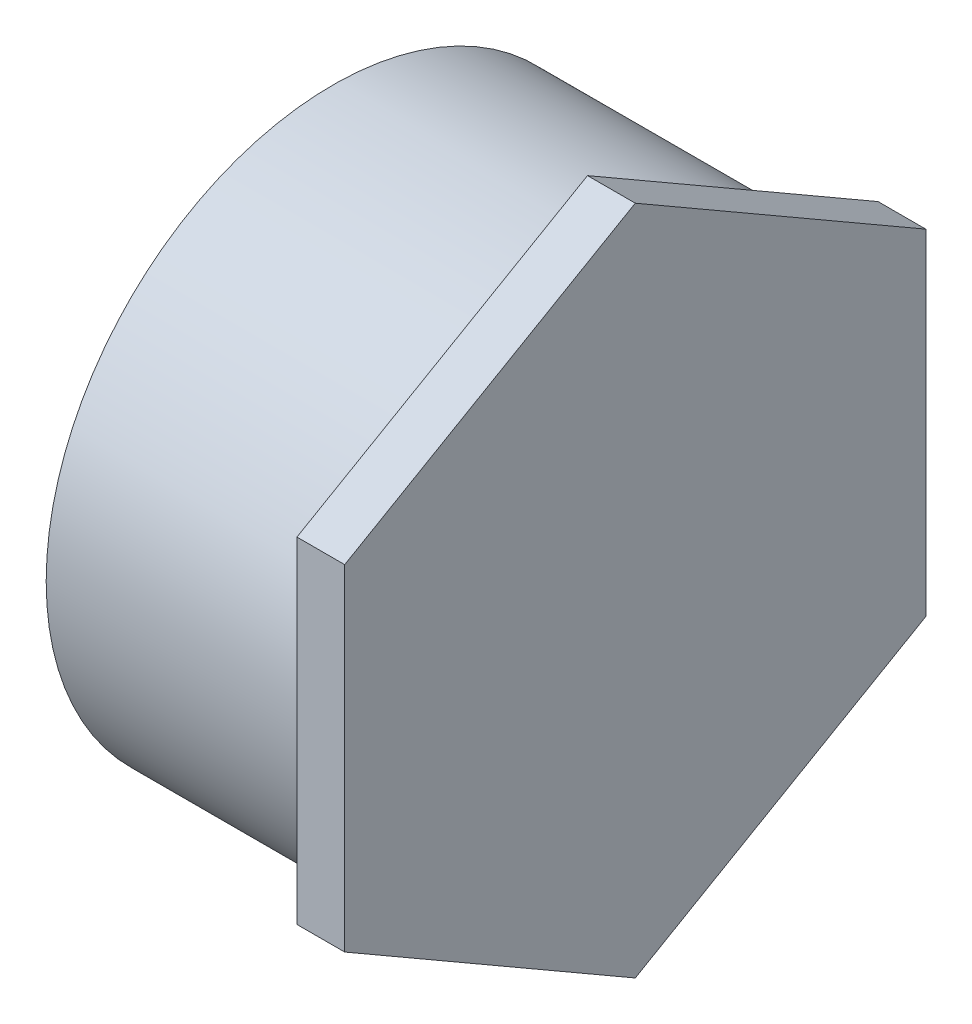
SolidWorks part; units mm, degrees
material "PVC Rigid"
ref_plane "Front Plane" through (0, 0, 0) normal (0, 0, 1) x (1, 0, 0)
ref_plane "Top Plane" through (0, 0, 0) normal (0, 1, 0) x (1, 0, 0)
ref_plane "Right Plane" through (0, 0, 0) normal (1, 0, 0) x (0, 0, -1)
sketch "Sketch0" plane through (0, 0, 0) normal (0, 0, 1) x (1, 0, 0)
  line L2 (-30.1625, 57.15) -> (-30.1625, -57.15) construction
  line L3 (-30.1625, 0) -> (30.1625, 0) construction
  line L14 (20.6375, 51.1302) -> (20.6375, -51.1302) construction
  point P5 (20.6375, 0)
  dimension "ID" = 102.2604
  dimension "L" = 60.325
  dimension "C" = 50.8
  dimension "Pipe OD" = 114.3
  dimension "R" = 9.525
  dimension "Wall Thickness" = 6.0198
sketch "Sketch1" plane through (0, 0, 0) normal (0, 0, 1) x (1, 0, 0)
  line L0 (-30.1625, -57.15) -> (30.1625, -57.15)
  line L1 (-30.1625, 0) -> (30.1625, 0) construction
  line L3 (30.1625, 0) -> (20.6375, 0)
  line L4 (20.6375, -51.1302) -> (-30.1625, -51.1302)
  line L5 (-30.1625, -51.1302) -> (-30.1625, -57.15)
  line L6 (-30.1625, 57.15) -> (-30.1625, -57.15) construction
  line L7 (30.1625, 0) -> (30.1625, -57.15)
  line L10 (20.6375, 0) -> (20.6375, -51.1302)
revolve "Revolve1" add sketch "Sketch1" angle 360 about L1
sketch "Sketch2" plane through (30.1625, 0, 0) normal (1, 0, 0) x (0, 0, -1)
  line L0 (0, 66.9077) -> (0, 0) construction
  line L1 (0, 66.9077) -> (-57.9437, 33.4538)
  line L2 (-57.9437, 33.4538) -> (-57.9437, -33.4538)
  line L3 (-57.9437, -33.4538) -> (0, -66.9077)
  line L4 (0, -66.9077) -> (57.9437, -33.4538)
  line L5 (57.9437, -33.4538) -> (57.9437, 33.4538)
  line L6 (57.9437, 33.4538) -> (0, 66.9077)
  circle A0 centre (0, 0) radius 57.9437 construction
  circle A1 centre (0, 0) radius 57.15
  circle A2 centre (0, 0) radius 57.15
  dimension "D2" = 115.8875
  dimension "D1" = 0
extrude "Boss-Extrude1" add sketch "Sketch2" against normal up to vertex (9.525 mm away) up to point (20.6375, 0, 0)
